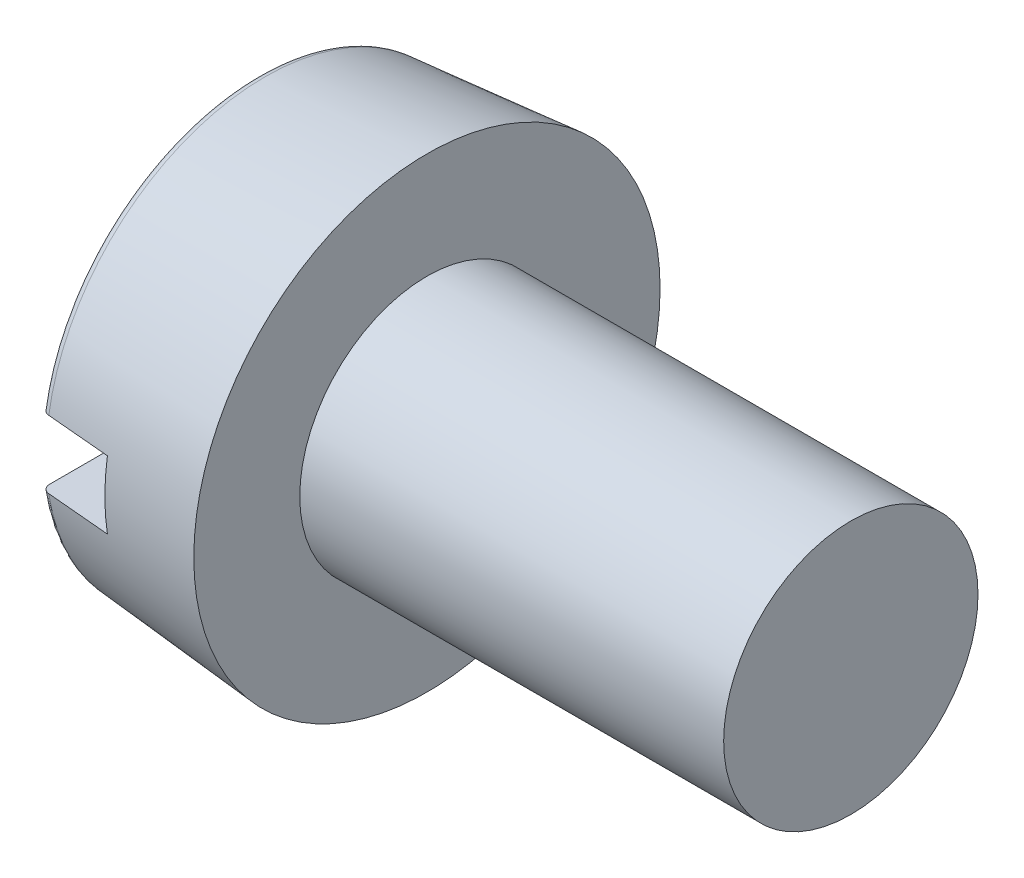
SolidWorks part; units mm, degrees
ref_plane "Plane1" through (0, 0, 0) normal (0, 0, 1) x (1, 0, 0)
ref_plane "Plane2" through (0, 0, 0) normal (0, 1, 0) x (1, 0, 0)
ref_plane "Plane3" through (0, 0, 0) normal (1, 0, 0) x (0, 0, -1)
sketch "BodySke" plane through (0, 0, 0) normal (0, 0, 1) x (1, 0, 0)
  line L0 (2, 1.5) -> (2, 2.75)
  line L1 (0, 0) -> (0, 2.575)
  line L2 (-25.4, 0) -> (127, 0) construction
  line L3 (7, 0) -> (0, 0)
  line L4 (2, 1.5) -> (7, 1.5)
  line L5 (7, 1.5) -> (7, 0)
  line L6 (0, 2.575) -> (2, 2.75)
  line L9 (2.5, 3.0875) -> (2.5, -6.4375) construction
  line L10 (2, 6.35) -> (2, -3.175) construction
  dimension "Head_ht" = 2
  dimension "Diameter" = 3
  dimension "Length" = 5
  dimension "Head_dia" = 5.5
  dimension "Advance" = 0.5
  dimension "Thread_nom" = 5
  dimension "Head_side_angle" = 5
revolve "Base-Revolve" add sketch "BodySke"
cosmetic thread "ThreadCosmetic" [suppressed]
fillet "Fillet1" [suppressed] radius 0.1
fillet "Fillet2" radius 0.1 1 edges at (0, 0, 2.575)
sketch "Sketch2" plane through (0, 0, 0) normal (1, 0, 0) x (0, 0, -1)
  line L0 (2.75, -0.4) -> (-2.75, -0.4)
  line L1 (2.75, -0.4) -> (2.75, 0.4)
  line L2 (-2.75, 0.4) -> (2.75, 0.4)
  line L3 (-2.75, 0.4) -> (-2.75, -0.4)
  dimension "D1" = 5.5
  dimension "D2" = 2.75
  dimension "Slot_width" = 0.8
  dimension "D3" = 0.4
extrude "Slot" cut sketch "Sketch2" along normal blind 0.85
sketch "ThdSchSke" plane through (0, 0, 0) normal (0, 0, 1) x (1, 0, 0)
  line L0 (3, -1.2195) -> (2.8036, -1.5)
  line L1 (3, -1.2195) -> (3.1964, -1.5)
  line L2 (3.1964, -1.5) -> (3.1964, -1.875)
  line L3 (-3.175, 0) -> (5.1513, 0) construction
  line L5 (3.1964, -1.875) -> (2.8036, -1.875)
  line L6 (2.8036, -1.875) -> (2.8036, -1.5)
  dimension "Thread_minor" = 2.439
  dimension "Diameter" = 3
  dimension "Start" = 3
  dimension "SideAngle" = 55
  dimension "VeeAngle" = 70
  dimension "Overcut" = 3.75
revolve "ThreadSchematic" [suppressed] cut sketch "ThdSchSke" angle 360 about L3
pattern_linear "ThdSchPat" [suppressed]
equation "\"D1@Sketch2\" = \"Head_dia@BodySke\""
equation "\"D2@Sketch2\" = \"D1@Sketch2\" / 2"
equation "\"D3@Sketch2\" = \"Slot_width@Sketch2\" / 2"
equation "\"Thread_length@ThreadCosmetic\" = ((sgn( (\"Length@BodySke\" - \"Advance@BodySke\" * 2.0 ) - \"Thread_nom@BodySke\" )-1)*( (\"Length@BodySke\" - \"Advance@BodySke\"  * 2.0) - \"Thread_nom@BodySke\" ))/-2+ \"Thread_nom@BodySke\""
equation "\"Thread_minor@ThdSchSke\" = \"Thread_minor@ThreadCosmetic\""
equation "\"Diameter@ThdSchSke\" = \"Diameter@BodySke\""
equation "\"Overcut@ThdSchSke\" = \"Diameter@BodySke\" * 1.25"
equation "\"Start@ThdSchSke\" = \"Head_ht@BodySke\" + \"Length@BodySke\" - \"Thread_length@ThreadCosmetic\"  '---Non-countersunk---"
equation "\"Num_threads@ThdSchPat\" = int( \"Thread_length@ThreadCosmetic\" / \"Advance@BodySke\" + 0.999 )  + 1"
equation "\"Advance@ThdSchPat\" = \"Thread_length@ThreadCosmetic\" /  (\"Num_threads@ThdSchPat\" - 1) 'relax it"
